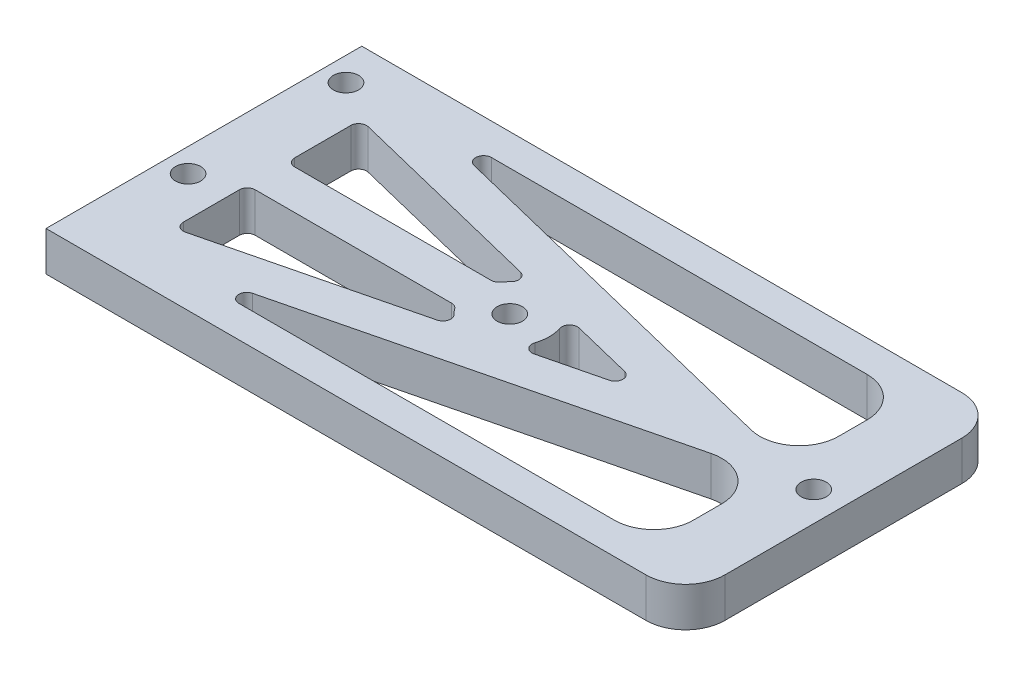
SolidWorks part; units mm, degrees
material "Thornel Mat VMA"
ref_plane "前视基准面" through (0, 0, 0) normal (0, 0, 1) x (1, 0, 0)
ref_plane "上视基准面" through (0, 0, 0) normal (0, 1, 0) x (1, 0, 0)
ref_plane "右视基准面" through (0, 0, 0) normal (1, 0, 0) x (0, 0, -1)
sketch "草图1" plane through (0, 0, 0) normal (0, 1, 0) x (1, 0, 0)
  line L1 (-40.5, 20) -> (40.5, 20)
  line L2 (-40.5, 20) -> (-40.5, -20)
  line L3 (-40.5, -20) -> (40.5, -20)
  line L4 (40.5, 20) -> (40.5, -20)
  line L5 (-40.5, 20) -> (40.5, -20) construction
  line L6 (-40.5, -20) -> (40.5, 20) construction
  point P0 (0, 0)
  dimension "D1" = 40
  dimension "D2" = 81
extrude "凸台-拉伸1" add sketch "草图1" along normal blind 5
sketch "草图2" plane through (0, 0, 0) normal (0, -1, 0) x (1, 0, 0)
  line L0 (36.75, 0) -> (-1.75, 0) construction
  line L1 (40.5, -20) -> (-40.5, -20) construction
  circle A0 centre (36.75, 0) radius 1.6
  circle A1 centre (-1.75, 0) radius 1.6
  dimension "D3" = 3.2
  dimension "D1" = 38.5
  dimension "D2" = 1.75
  dimension "D4" = 20
extrude "切除-拉伸1" cut sketch "草图2" against normal through all
fillet "圆角1" radius 5 2 edges at (40.5, 2.5, 20) (40.5, 2.5, -20)
sketch "草图3" plane through (0, 0, 0) normal (0, -1, 0) x (1, 0, 0)
  line L0 (-37.5, -15) -> (-37.5, 5) construction
  line L1 (-40.5, -20) -> (-40.5, 20) construction
  line L2 (35.5, -20) -> (-40.5, -20) construction
  circle A0 centre (-37.5, 5) radius 1.6
  circle A1 centre (-37.5, -15) radius 1.6
  dimension "D2" = 3.2
  dimension "D1" = 20
  dimension "D3" = 3
  dimension "D4" = 5
extrude "切除-拉伸2" cut sketch "草图3" against normal through all
sketch "草图4" plane through (0, 0, 0) normal (0, -1, 0) x (1, 0, 0)
  line L0 (-32.5, 16) -> (32.5, 0)
  line L1 (32.5, 0) -> (-32.5, -16)
  line L2 (-1.75, 0) -> (-35.5, 0)
  line L3 (-33.4561, 12.1159) -> (15.7649, 0)
  line L4 (-32.5, 16) -> (-32.5, -16)
  line L5 (32.5, -16) -> (32.5, 16)
  line L6 (-40.5, 20) -> (35.5, 20) construction
  line L7 (15.7649, 0) -> (-33.4561, -12.1159)
  line L8 (35.5, -15) -> (35.5, 15)
  line L9 (35.5, 15) -> (-35.5, 15)
  line L10 (-35.5, 15) -> (-35.5, -15)
  line L11 (-35.5, -15) -> (35.5, -15)
  line L12 (35.5, -16) -> (35.5, 16)
  line L13 (35.5, 16) -> (-35.5, 16)
  line L14 (-35.5, 16) -> (-35.5, -16)
  line L15 (-35.5, -16) -> (35.5, -16)
  line L16 (35.5, -20) -> (-40.5, -20) construction
  line L17 (-1.75, 2.5) -> (-35.5, 2.5)
  line L18 (-1.75, -2.5) -> (-35.5, -2.5)
  line L19 (-32.261, 16.971) -> (36.6838, 0)
  line L20 (36.6838, 0) -> (-32.261, -16.971)
  circle A2 centre (-1.75, 0) radius 5
  point P17 (-1.75, 0)
  point P21 (-32.5, 0)
  point P23 (-35.5, 0)
  point P24 (-38.1511, 0)
  dimension "D5" = 10
  dimension "D3" = 4
  dimension "D4" = 4
  dimension "D1" = 5
  dimension "D2" = 3
  dimension "D6" = 4
  dimension "D7" = 2.5
  dimension "D8" = 2.5
  dimension "D9" = 1
extrude "切除-拉伸5" cut sketch "草图4" against normal blind 10 contours A2 L3 L4 L17 | A2 L18 L4 L7 | A2 L7 L3 | L13 L19 L5 | L5 L20 L15
fillet "圆角2" radius 5 2 edges at (32.5, 2.5, 1.0299) (32.5, 2.5, -1.0299)
fillet "圆角3" radius 5 2 edges at (32.5, 2.5, 16) (32.5, 2.5, -16)
fillet "圆角4" radius 1 3 edges at (15.7649, 2.5, 0) (1.9053, 2.5, 3.4116) (1.9053, 2.5, -3.4116)
fillet "圆角5" radius 1 10 edges at (-32.5, 2.5, -11.8806) (-32.5, 2.5, -2.5) (-6.0801, 2.5, -2.5) (-3.404, 2.5, -4.7185) (-32.5, 2.5, 2.5) (-3.404, 2.5, 4.7185) (-6.0801, 2.5, 2.5) (-28.3162, 2.5, -16) (-28.3162, 2.5, 16) (-32.5, 2.5, 11.8806)
